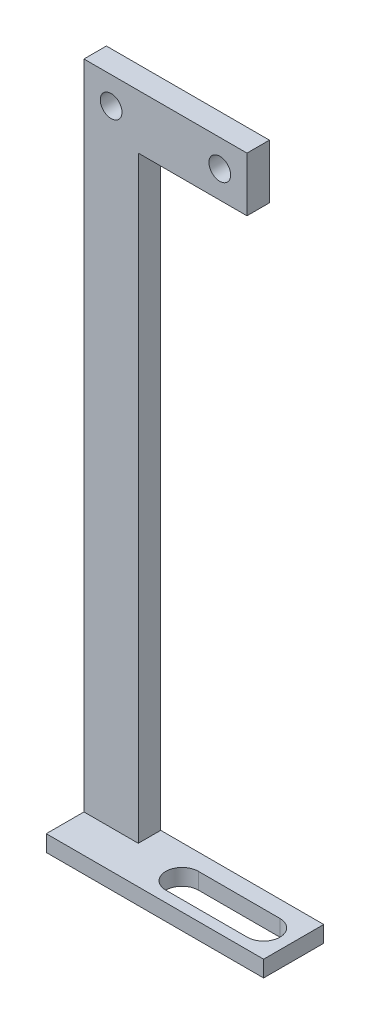
SolidWorks part; units mm, degrees
ref_plane "前视基准面" through (0, 0, 0) normal (0, 0, 1) x (1, 0, 0)
ref_plane "上视基准面" through (0, 0, 0) normal (0, 1, 0) x (1, 0, 0)
ref_plane "右视基准面" through (0, 0, 0) normal (1, 0, 0) x (0, 0, -1)
sketch "草图1" plane through (0, 0, 0) normal (0, 1, 0) x (1, 0, 0)
  line L0 (0, 0) -> (0, -10)
  line L1 (0, -10) -> (25, -10)
  line L2 (25, -10) -> (25, 0)
  line L3 (25, 0) -> (0, 0)
  line L4 (0, -5) -> (5, -5)
  line L5 (25, -5) -> (20, -5)
  line L6 (5, -5) -> (20, -5) construction
  line L7 (5, -2) -> (20, -2)
  line L8 (5, -8) -> (20, -8)
  arc A0 (5, -2) -> (5, -8) centre (5, -5) ccw
  arc A1 (20, -8) -> (20, -2) centre (20, -5) ccw
  point P9 (12.5, -5)
extrude "凸台-拉伸1" add sketch "草图1" along normal blind 3 contours A1 L5 L2 L3 L0 L4 A0 L7 | A1 L8 A0 L4 L0 L1 L2 L5
sketch "草图4" plane through (0, 3, 0) normal (0, 1, 0) x (1, 0, 0)
  line L0 (0, 0) -> (-15, 0)
  line L1 (-15, 0) -> (-15, -10)
  line L2 (-15, -10) -> (0, -10)
  line L3 (0, 0) -> (0, -10)
extrude "凸台-拉伸3" add sketch "草图4" against normal blind 3 contours L0 L1 L2 L3
sketch "草图5" plane through (0, 3, 0) normal (0, 1, 0) x (1, 0, 0)
  line L0 (-15, 1.0647) -> (-15, -3.0647)
  line L1 (-15, 0) -> (-15, -10) construction
  line L2 (-15, -3.0647) -> (-5, -3.0647)
  line L3 (-5, -3.0647) -> (-5, 1.0647)
  line L4 (-5, 1.0647) -> (-15, 1.0647)
  point P5 (-15, -1)
extrude "凸台-拉伸4" add sketch "草图5" along normal blind 120 and the other way through all
sketch "草图6" plane through (0, 0, 3.0647) normal (0, 0, 1) x (1, 0, 0)
  line L0 (-10, 123) -> (-10, 118)
  line L1 (-5, 123) -> (-15, 123) construction
  circle A0 centre (-10, 118) radius 2
extrude "切除-拉伸2" cut sketch "草图6" against normal through all contours A0
sketch "草图7" plane through (-5, 0, 0) normal (1, 0, 0) x (0, 0, -1)
  line L0 (0, 3) -> (1.0647, 3)
  line L1 (1.0647, 0) -> (1.0647, 123) construction
  line L2 (1.0647, 3) -> (1.0647, 0)
  line L3 (1.0647, 0) -> (0, 0)
  line L4 (0, 0) -> (0, 3)
extrude "凸台-拉伸5" add sketch "草图7" along normal through all
sketch "草图8" plane through (-5, 0, 0) normal (1, 0, 0) x (0, 0, -1)
  line L0 (-3.0647, 123) -> (-3.0647, 113)
  line L1 (-3.0647, 3) -> (-3.0647, 123) construction
  line L2 (-3.0647, 113) -> (1.0647, 113)
  line L3 (1.0647, 3) -> (1.0647, 123) construction
  line L4 (1.0647, 113) -> (1.0647, 123)
  line L5 (1.0647, 123) -> (-3.0647, 123)
extrude "凸台-拉伸6" add sketch "草图8" along normal blind 20
sketch "草图9" plane through (0, 0, 3.0647) normal (0, 0, 1) x (1, 0, 0)
  line L0 (-10, 118) -> (10, 118)
  circle A0 centre (10, 118) radius 2
  point P3 (9.6455, 83)
  point P5 (0, 0)
extrude "切除-拉伸3" cut sketch "草图9" against normal through all contours A0
